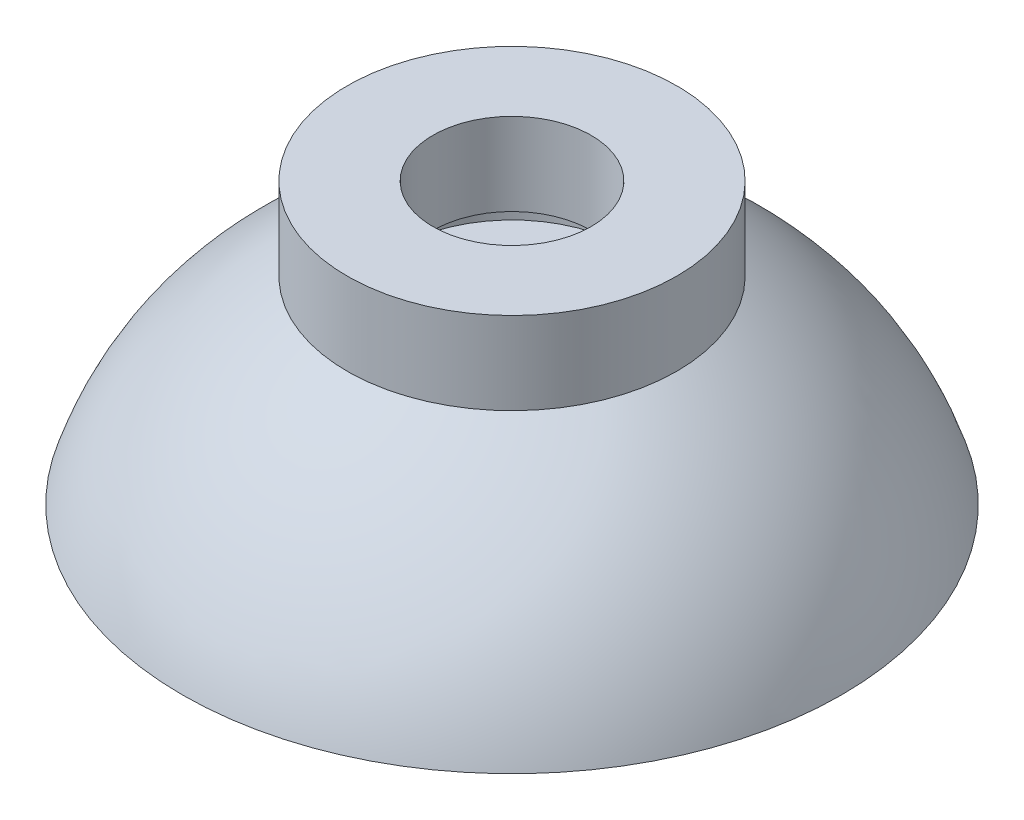
SolidWorks part; units mm, degrees
ref_plane "Front Plane" through (0, 0, 0) normal (0, 0, 1) x (1, 0, 0)
ref_plane "Top Plane" through (0, 0, 0) normal (0, 1, 0) x (1, 0, 0)
ref_plane "Right Plane" through (0, 0, 0) normal (1, 0, 0) x (0, 0, -1)
sketch "Sketch2" plane through (0, 0, 0) normal (0, 0, 1) x (1, 0, 0)
  line L0 (-1018.9479, 0) -> (49928.4451, 0) construction
  line L1 (0, -1018.9479) -> (0, 1.5) construction
  line L2 (0, -8.5) -> (20, -8.5)
  line L3 (4.8, 8.5) -> (10, 8.5)
  line L4 (10, 8.5) -> (10, 3.5)
  line L6 (4.8, 3.5) -> (7, 3.5)
  line L7 (7, 3.5) -> (7, 1.5)
  line L8 (7, 1.5) -> (0, 1.5)
  line L9 (0, 1.5) -> (0, -8.5)
  line L10 (4.8, 3.5) -> (4.8, 8.5)
  spline S0 degree 2 poles (10, 3.5) (17.6708, -1.0034) (20, -8.5) knots 0 0 0 1 1 1
  dimension "D6" = 16
  dimension "D1" = 20
  dimension "D2" = 7
  dimension "D3" = 2
  dimension "D4" = 5
  dimension "D7" = 10
  dimension "D8" = 5.2
revolve "Revolve3" add sketch "Sketch2" angle 360 about L1
